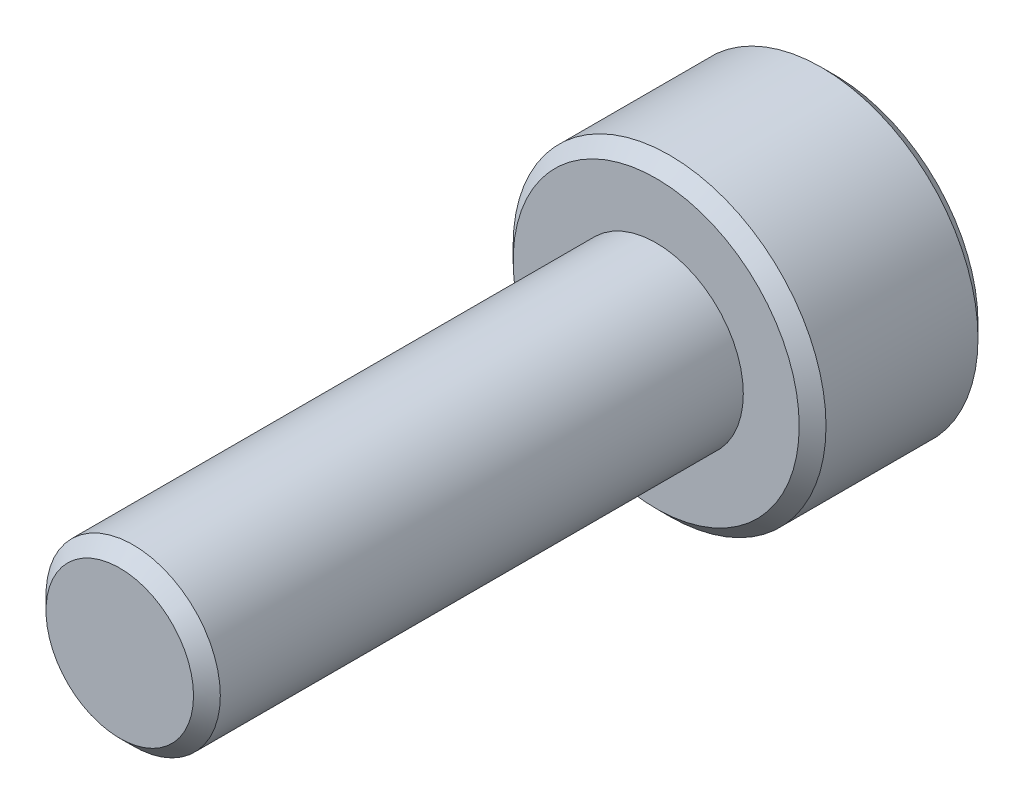
SolidWorks part; units mm, degrees
material "AISI 1020"
ref_plane "Front" through (0, 0, 0) normal (0, 0, 1) x (1, 0, 0)
ref_plane "Top" through (0, 0, 0) normal (0, 1, 0) x (1, 0, 0)
ref_plane "Right" through (0, 0, 0) normal (1, 0, 0) x (0, 0, -1)
sketch "Skizze1" plane through (0, 0, 0) normal (0, 0, 1) x (1, 0, 0)
  circle A0 centre (0, 0) radius 3.5
  dimension "D1" = 7
extrude "Aufsatz-Linear austragen1" add sketch "Skizze1" along normal blind 4
sketch "Skizze2" plane through (0, 0, 4) normal (0, 0, 1) x (1, 0, 0)
  circle A0 centre (0, 0) radius 1.95
  dimension "D1" = 3.9
extrude "Aufsatz-Linear austragen2" add sketch "Skizze2" along normal blind 12
chamfer "Fase1" distance 0.3 angle 45 3 edges at (3.5, 0, 4) (3.5, 0, 0) (1.95, 0, 16)
sketch "Skizze3" plane through (0, 0, 0) normal (0, 0, -1) x (-1, 0, 0)
  line L0 (1.5, 0) -> (0, 0) construction
  line L1 (1.5, 0.866) -> (0, 1.7321)
  line L2 (0, 1.7321) -> (-1.5, 0.866)
  line L3 (-1.5, 0.866) -> (-1.5, -0.866)
  line L4 (-1.5, -0.866) -> (0, -1.7321)
  line L5 (0, -1.7321) -> (1.5, -0.866)
  line L6 (1.5, -0.866) -> (1.5, 0.866)
  circle A0 centre (0, 0) radius 1.5 construction
  dimension "D1" = 3
extrude "Schnitt-Linear austragen1" cut sketch "Skizze3" against normal blind 2.5
